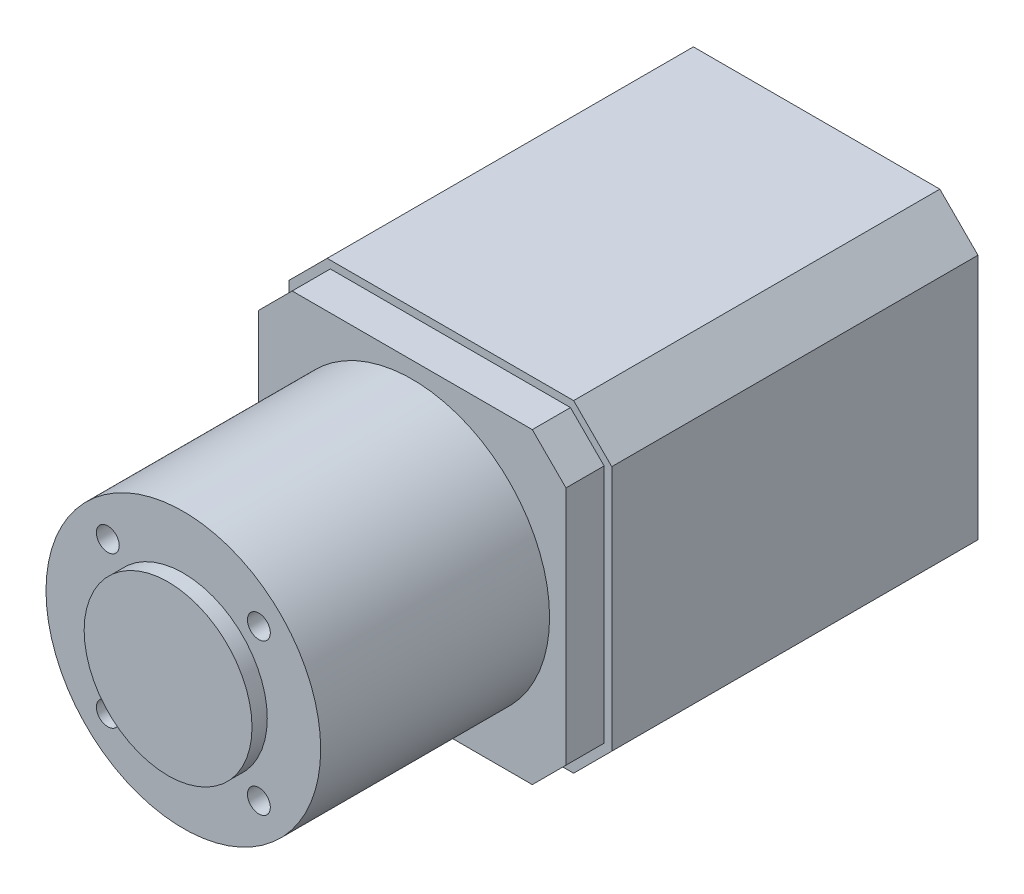
SolidWorks part; units mm, degrees
ref_plane "Piano frontale" through (0, 0, 0) normal (0, 0, 1) x (1, 0, 0)
ref_plane "Piano superiore" through (0, 0, 0) normal (0, 1, 0) x (1, 0, 0)
ref_plane "Piano destro" through (0, 0, 0) normal (1, 0, 0) x (0, 0, -1)
sketch "Schizzo1" plane through (0, 0, 0) normal (0, 0, 1) x (1, 0, 0)
  line L1 (21.15, -21.15) -> (-21.15, -21.15)
  line L2 (21.15, -21.15) -> (21.15, 21.15)
  line L3 (21.15, 21.15) -> (-21.15, 21.15)
  line L4 (-21.15, -21.15) -> (-21.15, 21.15)
  line L5 (21.15, -21.15) -> (-21.15, 21.15) construction
  line L6 (21.15, 21.15) -> (-21.15, -21.15) construction
  point P0 (0, 0)
  dimension "D1" = 42.3
  dimension "D2" = 42.3
extrude "Estrusione-Estrusione1" add sketch "Schizzo1" along normal blind 48
chamfer "Smusso1" distance 5 angle 45 4 edges at (-21.15, -21.15, 24) (21.15, -21.15, 24) (21.15, 21.15, 24) (-21.15, 21.15, 24)
sketch "Schizzo2" plane through (0, 0, 48) normal (0, 0, 1) x (1, 0, 0)
  line L17 (-20.15, 15.7358) -> (-20.15, -15.7358)
  line L18 (-20.15, -15.7358) -> (-15.7358, -20.15)
  line L19 (-15.7358, -20.15) -> (15.7358, -20.15)
  line L20 (15.7358, -20.15) -> (20.15, -15.7358)
  line L21 (20.15, -15.7358) -> (20.15, 15.7358)
  line L22 (20.15, 15.7358) -> (15.7358, 20.15)
  line L23 (15.7358, 20.15) -> (-15.7358, 20.15)
  line L24 (-15.7358, 20.15) -> (-20.15, 15.7358)
  line L25 (-20.15, 15.7358) -> (-20.15, -15.7358)
  line L26 (-20.15, -15.7358) -> (-15.7358, -20.15)
  line L27 (-15.7358, -20.15) -> (15.7358, -20.15)
  line L28 (15.7358, -20.15) -> (20.15, -15.7358)
  line L29 (20.15, -15.7358) -> (20.15, 15.7358)
  line L30 (20.15, 15.7358) -> (15.7358, 20.15)
  line L31 (15.7358, 20.15) -> (-15.7358, 20.15)
  line L32 (-15.7358, 20.15) -> (-20.15, 15.7358)
  dimension "D1" = 1
extrude "Estrusione-Estrusione2" add sketch "Schizzo2" along normal blind 5
sketch "Schizzo3" plane through (0, 0, 53) normal (0, 0, 1) x (1, 0, 0)
  circle A0 centre (0, 0) radius 18
  dimension "D1" = 36
extrude "Estrusione-Estrusione3" add sketch "Schizzo3" along normal blind 30
sketch "Schizzo4" plane through (0, 0, 83) normal (0, 0, 1) x (1, 0, 0)
  circle A0 centre (0, 0) radius 11
  dimension "D1" = 22
extrude "Estrusione-Estrusione4" add sketch "Schizzo4" along normal blind 2
sketch "Schizzo7" plane through (0, 0, 83) normal (0, 0, 1) x (1, 0, 0)
  line L0 (0, -21.15) -> (0, 21.15) construction
  line L1 (-16.15, -21.15) -> (16.15, -21.15) construction
  line L2 (16.15, 21.15) -> (-16.15, 21.15) construction
  line L3 (0, 0) -> (9.8995, 9.8995) construction
  circle A0 centre (9.8995, 9.8995) radius 1.5
  dimension "D2" = 3
  dimension "D1" = 14
  dimension "D3" = 45
extrude "Taglio-Estrusione2" cut sketch "Schizzo7" against normal up to surface (30 mm away) up to face at (18, 0, 53)
pattern_circular "RipetizioneCircolare1" count 4 every 90 about axis through (0, 0, 0) along (0, 0, 1) of "Taglio-Estrusione2"
